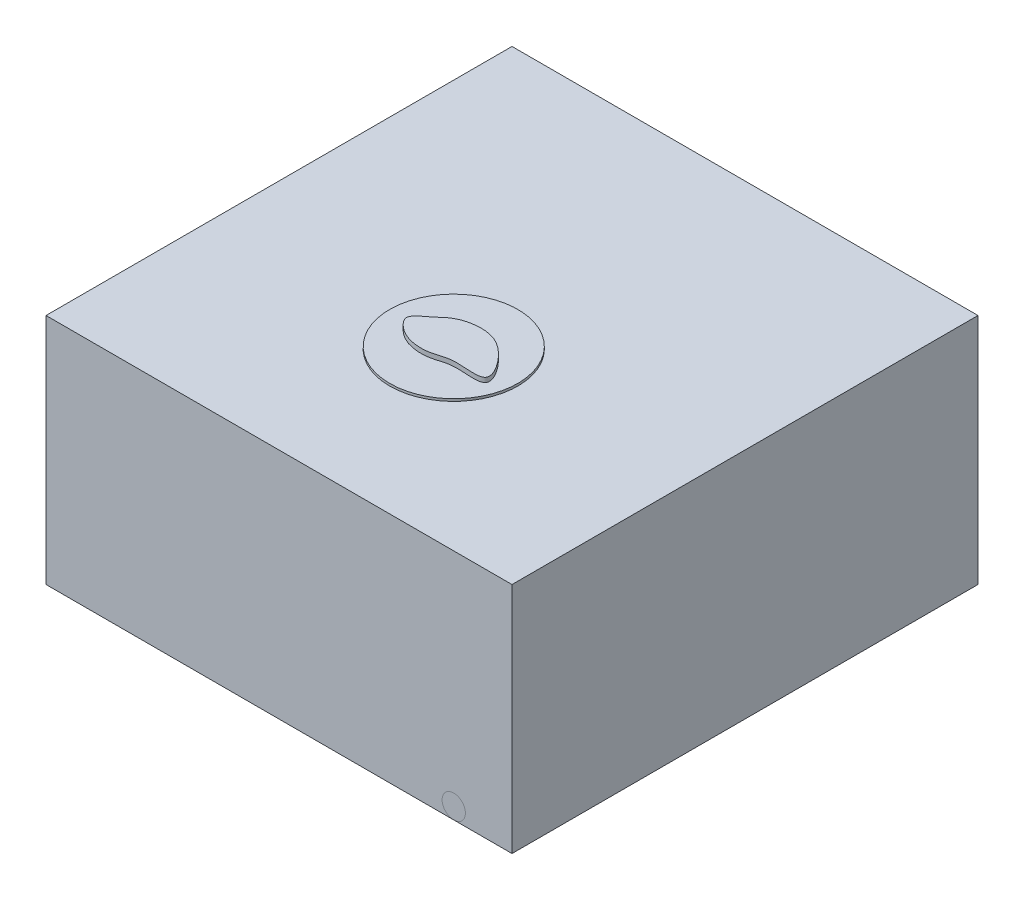
SolidWorks part; units mm, degrees
ref_plane "Front Plane" through (0, 0, 0) normal (0, 0, 1) x (1, 0, 0)
ref_plane "Top Plane" through (0, 0, 0) normal (0, 1, 0) x (1, 0, 0)
ref_plane "Right Plane" through (0, 0, 0) normal (1, 0, 0) x (0, 0, -1)
sketch "Sketch1" plane through (0, 0, 0) normal (0, 0, 1) x (1, 0, 0)
  line L1 (-10, -5) -> (10, -5)
  line L2 (-10, -5) -> (-10, 5)
  line L3 (-10, 5) -> (10, 5)
  line L4 (10, -5) -> (10, 5)
  line L5 (0, 5) -> (0, -5) construction
  line L6 (-10, 0) -> (10, 0) construction
  point P0 (0, 0)
  dimension "D1" = 20
  dimension "D2" = 10
extrude "Boss-Extrude1" add sketch "Sketch1" along normal blind 20
sketch "Sketch2" plane through (0, 0, 20) normal (0, 0, 1) x (1, 0, 0)
  line L0 (-10, -5) -> (10, -5) construction
  line L1 (0, 0) -> (0, -5) construction
  circle A0 centre (-7.5, -4.5) radius 0.5
  circle A1 centre (7.5, -4.5) radius 0.5
  dimension "D1" = 1
  dimension "D2" = 7.5
ref_plane "Plane1" through (7.5, 0, 0) normal (1, 0, 0) x (0, 0, -1)
sketch "Sketch3" plane through (7.5, 0, 0) normal (1, 0, 0) x (0, 0, -1)
  line L3 (-20, -4.5) -> (-5, -4.5)
  line L7 (-20, -4) -> (-20, -5) construction
  line L8 (-4, -3.5) -> (-4, 5)
  line L9 (-20, 5) -> (0, 5) construction
  arc A0 (-5, -4.5) -> (-4, -3.5) centre (-5, -3.5) ccw
  dimension "D1" = 1
  dimension "D2" = 15
sweep "ag/agcl electrodes" add profiles "Sketch2" path "Sketch3"
sketch "Sketch5" plane through (0, 5, 0) normal (0, 1, 0) x (1, 0, 0)
  line L0 (0, -12.5) -> (2.75, -12.5) construction
  line L2 (0, -12.5) -> (0, -9.75) construction
  line L3 (-10, -20) -> (-10, 0) construction
  line L5 (10, -20) -> (-10, -20) construction
  circle A0 centre (0, -12.5) radius 2.75
  dimension "D1" = 5.5
  dimension "D2" = 10
  dimension "D3" = 7.5
extrude "Boss-Extrude4" add sketch "Sketch5" along normal blind 0.1 separate body
sketch "Sketch8" plane through (0, 5.1, 0) normal (0, -1, 0) x (-1, 0, 0)
  line L0 (0, -12.5) -> (2.75, -12.5) construction
  line L2 (0, -12.5) -> (0, -9.75) construction
  circle A1 centre (0, -12.5) radius 0.005
  circle A2 centre (0.5, -12.5) radius 0.005
  circle A3 centre (0.5, -12) radius 0.005
  circle A4 centre (0, -12) radius 0.005
  circle A5 centre (0.5, -13) radius 0.005
  circle A6 centre (0, -13) radius 0.005
  circle A7 centre (-0.5, -13) radius 0.005
  circle A8 centre (-0.5, -12) radius 0.005
  circle A9 centre (-0.5, -12.5) radius 0.005
  circle A10 centre (0, -12.5) radius 2.75 construction
  dimension "D1" = 0.5
  dimension "D2" = 0.01
  dimension "D5" = 0.5
  dimension "D3" = 2
  dimension "D4" = 2
extrude "Boss-Extrude5" add sketch "Sketch8" along normal blind 0.1 separate body
sketch "Sketch4" plane through (0, 5, 0) normal (0, 1, 0) x (1, 0, 0)
  line L0 (0, -11.4373) -> (0, -13.4201) construction
  line L1 (-2.0803, -12.5) -> (1.6023, -12.5) construction
  spline S0 degree 3 poles (-2.0861, -12.5392) (-1.3776, -12.1296) (-0.8241, -11.549) (0.2513, -11.3226) (1.3726, -11.7466) (2.6529, -13.5718) (0.7805, -13.1045) (-0.1221, -13.5063) (-0.9948, -13.461) (-1.5864, -13.1169) (-2.0861, -12.5392) (-1.3776, -12.1296) (-0.8241, -11.549) knots -0.204834 -0.133435 -0.089031 0 0.049563 0.182818 0.303261 0.461561 0.613381 0.684438 0.795166 0.866565 0.910969 1 1.049563 1.182818 1.303261 only from (-1.3298, -12.0471) to (-1.3298, -12.0471)
extrude "slice" add sketch "Sketch4" along normal blind 0.3 separate body
